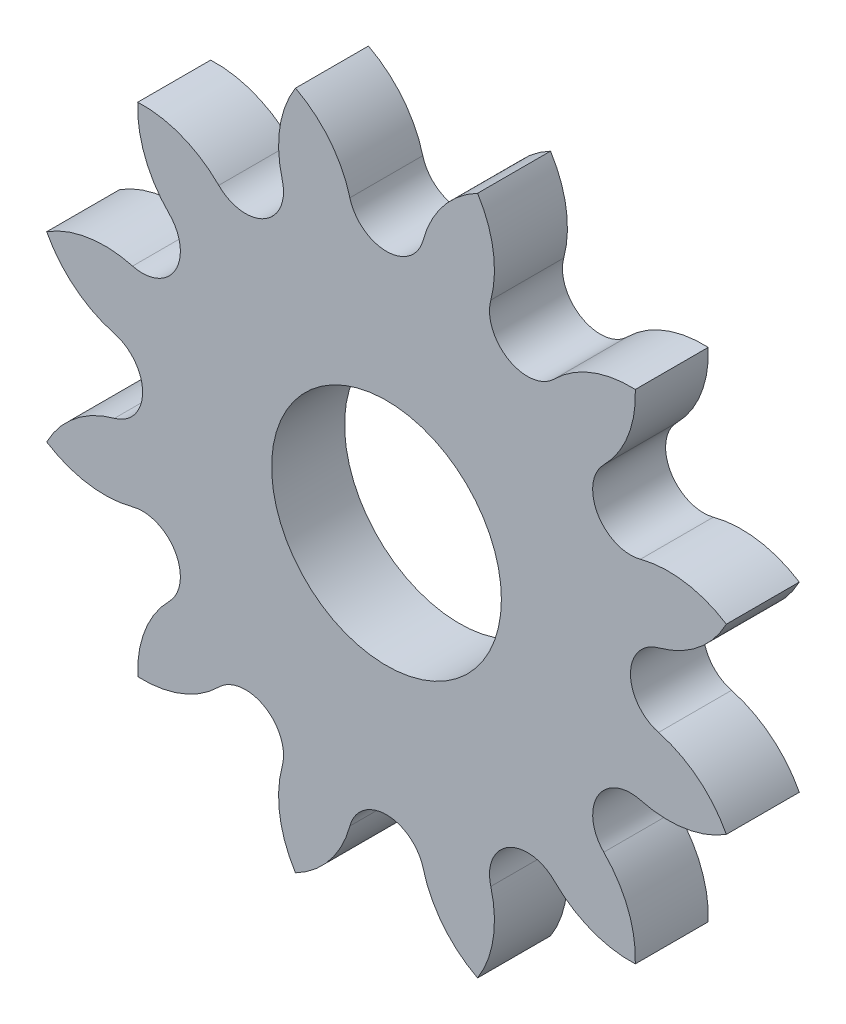
SolidWorks part; units mm, degrees
ref_plane "Front Plane" through (0, 0, 0) normal (0, 0, 1) x (1, 0, 0)
ref_plane "Top Plane" through (0, 0, 0) normal (0, 1, 0) x (1, 0, 0)
ref_plane "Right Plane" through (0, 0, 0) normal (1, 0, 0) x (0, 0, -1)
sketch "Sketch2" plane through (0, 0, 0) normal (0, 0, 1) x (1, 0, 0)
  arc A0 (9.4568, 7.3021) -> (10.8287, 10.828) centre (6.1341, 10.6248) ccw
  arc A1 (10.8287, 10.828) -> (7.3015, 9.4574) centre (10.6231, 6.1336) ccw
  arc A2 (4.5392, 11.0515) -> (7.3015, 9.4574) centre (6.1341, 10.6248) ccw
  arc A3 (4.5392, 11.0515) -> (3.9641, 14.7915) centre (0.0003, 12.2677) ccw
  arc A4 (3.9641, 14.7915) -> (1.5953, 11.8414) centre (6.1337, 10.6234) ccw
  arc A5 (-1.5945, 11.8414) -> (1.5953, 11.8414) centre (0.0004, 12.2681) ccw
  arc A6 (-1.5945, 11.8414) -> (-3.9614, 14.7915) centre (-6.1332, 10.6244) ccw
  arc A7 (-3.9614, 14.7915) -> (-4.5384, 11.0515) centre (0.0011, 12.2657) ccw
  arc A8 (-7.3007, 9.4574) -> (-4.5384, 11.0515) centre (-6.1333, 10.6248) ccw
  arc A9 (-7.3007, 9.4574) -> (-10.8272, 10.8287) centre (-10.6229, 6.1341) ccw
  arc A10 (-10.8272, 10.8287) -> (-9.456, 7.3021) centre (-6.1327, 10.6242) ccw
  arc A11 (-11.0501, 4.5398) -> (-9.456, 7.3021) centre (-10.6234, 6.1347) ccw
  arc A12 (-11.0501, 4.5398) -> (-14.7901, 3.9646) centre (-12.2663, 0.0009) ccw
  arc A13 (-14.7901, 3.9646) -> (-11.84, 1.5959) centre (-10.6219, 6.1343) ccw
  arc A14 (-11.84, -1.5939) -> (-11.84, 1.5959) centre (-12.2667, 0.001) ccw
  arc A15 (-11.84, -1.5939) -> (-14.79, -3.9608) centre (-10.623, -6.1326) ccw
  arc A16 (-14.79, -3.9608) -> (-11.0501, -4.5378) centre (-12.2643, 0.0016) ccw
  arc A17 (-9.456, -7.3001) -> (-11.0501, -4.5378) centre (-10.6234, -6.1327) ccw
  arc A18 (-9.456, -7.3001) -> (-10.8273, -10.8266) centre (-6.1327, -10.6223) ccw
  arc A19 (-10.8273, -10.8266) -> (-7.3007, -9.4554) centre (-10.6228, -6.1321) ccw
  arc A20 (-4.5384, -11.0495) -> (-7.3007, -9.4554) centre (-6.1333, -10.6228) ccw
  arc A21 (-4.5384, -11.0495) -> (-3.9632, -14.7895) centre (0.0005, -12.2657) ccw
  arc A22 (-3.9632, -14.7895) -> (-1.5945, -11.8394) centre (-6.1329, -10.6214) ccw
  arc A23 (1.5953, -11.8394) -> (-1.5945, -11.8394) centre (0.0004, -12.2661) ccw
  arc A24 (1.5953, -11.8394) -> (3.9622, -14.7894) centre (6.134, -10.6224) ccw
  arc A25 (3.9622, -14.7894) -> (4.5392, -11.0495) centre (-0.0002, -12.2637) ccw
  arc A26 (7.3015, -9.4554) -> (4.5392, -11.0495) centre (6.1341, -10.6228) ccw
  arc A27 (7.3015, -9.4554) -> (10.828, -10.8267) centre (10.6237, -6.1321) ccw
  arc A28 (10.828, -10.8267) -> (9.4568, -7.3001) centre (6.1335, -10.6222) ccw
  arc A29 (11.0509, -4.5378) -> (9.4568, -7.3001) centre (10.6242, -6.1327) ccw
  arc A30 (11.0509, -4.5378) -> (14.7909, -3.9626) centre (12.2671, 0.0011) ccw
  arc A31 (14.7909, -3.9626) -> (11.8408, -1.5939) centre (10.6228, -6.1323) ccw
  arc A32 (11.8414, 1.5953) -> (11.8408, -1.5939) centre (12.2689, 0.0006) ccw
  arc A33 (11.8414, 1.5953) -> (14.7915, 3.9622) centre (10.6244, 6.134) ccw
  arc A34 (14.7915, 3.9622) -> (11.0515, 4.5392) centre (12.2657, -0.0002) ccw
  arc A35 (9.4568, 7.3021) -> (11.0515, 4.5392) centre (10.6232, 6.1337) ccw
  circle A36 centre (0, 0) radius 5
  dimension "D1" = 10
extrude "Boss-Extrude2" add sketch "Sketch2" along normal blind 3.175
